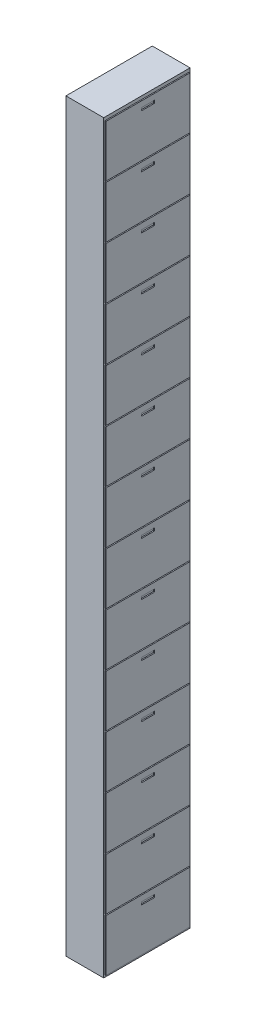
SolidWorks part; units mm, degrees
ref_plane "Front Plane" through (0, 0, 0) normal (0, 0, 1) x (1, 0, 0)
ref_plane "Top Plane" through (0, 0, 0) normal (0, 1, 0) x (1, 0, 0)
ref_plane "Right Plane" through (0, 0, 0) normal (1, 0, 0) x (0, 0, -1)
sketch "Sketch1" plane through (0, 0, 0) normal (0, 0, 1) x (1, 0, 0)
  line L0 (213.062, 4179.9863) -> (-136.938, 4179.9863)
  line L1 (-136.938, 4179.9863) -> (-136.938, -2720.0137)
  line L2 (-136.938, -2720.0137) -> (213.062, -2720.0137)
  line L5 (213.062, -2720.0137) -> (213.062, 4179.9863)
  dimension "D1" = 350
  dimension "D2" = 6900
extrude "Boss-Extrude1" add sketch "Sketch1" along normal blind 800
sketch "Sketch3" plane through (213.062, 0, 0) normal (1, 0, 0) x (0, 0, -1)
  line L0 (0, -2720.0137) -> (0, 4179.9863) construction
  line L1 (-790, -2700.0137) -> (-10, -2700.0137)
  line L2 (-790, -2700.0137) -> (-790, -2220.0137)
  line L3 (-790, -2220.0137) -> (-10, -2220.0137)
  line L4 (-10, -2700.0137) -> (-10, -2220.0137)
  line L5 (-800, -2720.0137) -> (0, -2720.0137) construction
  line L6 (-790, -2210.0137) -> (-10, -2210.0137)
  line L7 (-461.6648, -2274.1108) -> (-340.5919, -2274.1108)
  line L8 (-461.6648, -2274.1108) -> (-461.6648, -2299.9132)
  line L9 (-461.6648, -2299.9132) -> (-340.5919, -2299.9132)
  line L10 (-340.5919, -2274.1108) -> (-340.5919, -2299.9132)
  line L11 (-790, -2210.0137) -> (-790, -1730.0137)
  line L12 (-790, -1730.0137) -> (-10, -1730.0137)
  line L13 (-10, -2210.0137) -> (-10, -1730.0137)
  line L14 (-461.6648, -1784.1108) -> (-340.5919, -1784.1108)
  line L15 (-461.6648, -1809.9132) -> (-340.5919, -1809.9132)
  line L16 (-461.6648, -1784.1108) -> (-461.6648, -1809.9132)
  line L17 (-340.5919, -1784.1108) -> (-340.5919, -1809.9132)
  line L18 (-790, -1720.0137) -> (-10, -1720.0137)
  line L19 (-790, -1720.0137) -> (-790, -1240.0137)
  line L20 (-790, -1240.0137) -> (-10, -1240.0137)
  line L21 (-10, -1720.0137) -> (-10, -1240.0137)
  line L22 (-461.6648, -1294.1108) -> (-340.5919, -1294.1108)
  line L23 (-461.6648, -1319.9132) -> (-340.5919, -1319.9132)
  line L24 (-461.6648, -1294.1108) -> (-461.6648, -1319.9132)
  line L25 (-340.5919, -1294.1108) -> (-340.5919, -1319.9132)
  line L26 (-790, -1230.0137) -> (-10, -1230.0137)
  line L27 (-790, -1230.0137) -> (-790, -750.0137)
  line L28 (-790, -750.0137) -> (-10, -750.0137)
  line L29 (-10, -1230.0137) -> (-10, -750.0137)
  line L30 (-461.6648, -804.1108) -> (-340.5919, -804.1108)
  line L31 (-461.6648, -829.9132) -> (-340.5919, -829.9132)
  line L32 (-800, -2720.0137) -> (-800, 4179.9863) construction
  line L34 (-461.6648, -804.1108) -> (-461.6648, -829.9132)
  line L35 (-340.5919, -804.1108) -> (-340.5919, -829.9132)
  line L36 (-790, -740.0137) -> (-10, -740.0137)
  line L37 (-790, -740.0137) -> (-790, -260.0137)
  line L38 (-790, -260.0137) -> (-10, -260.0137)
  line L39 (-10, -740.0137) -> (-10, -260.0137)
  line L40 (-461.6648, -314.1108) -> (-340.5919, -314.1108)
  line L41 (-461.6648, -339.9132) -> (-340.5919, -339.9132)
  line L42 (-461.6648, -314.1108) -> (-461.6648, -339.9132)
  line L43 (-340.5919, -314.1108) -> (-340.5919, -339.9132)
  line L44 (-790, -250.0137) -> (-10, -250.0137)
  line L45 (-790, -250.0137) -> (-790, 229.9863)
  line L46 (-790, 229.9863) -> (-10, 229.9863)
  line L47 (-10, -250.0137) -> (-10, 229.9863)
  line L48 (-461.6648, 175.8892) -> (-340.5919, 175.8892)
  line L49 (-461.6648, 150.0868) -> (-340.5919, 150.0868)
  line L50 (-461.6648, 175.8892) -> (-461.6648, 150.0868)
  line L51 (-340.5919, 175.8892) -> (-340.5919, 150.0868)
  line L52 (-790, 239.9863) -> (-10, 239.9863)
  line L53 (-790, 239.9863) -> (-790, 719.9863)
  line L54 (-790, 719.9863) -> (-10, 719.9863)
  line L55 (-10, 239.9863) -> (-10, 719.9863)
  line L56 (-461.6648, 665.8892) -> (-340.5919, 665.8892)
  line L57 (-461.6648, 640.0868) -> (-340.5919, 640.0868)
  line L58 (-461.6648, 665.8892) -> (-461.6648, 640.0868)
  line L59 (-340.5919, 665.8892) -> (-340.5919, 640.0868)
  line L60 (-790, 729.9863) -> (-10, 729.9863)
  line L61 (-790, 729.9863) -> (-790, 1209.9863)
  line L62 (-790, 1209.9863) -> (-10, 1209.9863)
  line L63 (-10, 729.9863) -> (-10, 1209.9863)
  line L64 (-461.6648, 1155.8892) -> (-340.5919, 1155.8892)
  line L65 (-461.6648, 1130.0868) -> (-340.5919, 1130.0868)
  line L66 (-461.6648, 1155.8892) -> (-461.6648, 1130.0868)
  line L67 (-340.5919, 1155.8892) -> (-340.5919, 1130.0868)
  line L68 (-790, 1219.9863) -> (-10, 1219.9863)
  line L69 (-790, 1219.9863) -> (-790, 1699.9863)
  line L70 (-790, 1699.9863) -> (-10, 1699.9863)
  line L71 (-10, 1219.9863) -> (-10, 1699.9863)
  line L72 (-461.6648, 1645.8892) -> (-340.5919, 1645.8892)
  line L73 (-461.6648, 1620.0868) -> (-340.5919, 1620.0868)
  line L74 (-461.6648, 1645.8892) -> (-461.6648, 1620.0868)
  line L75 (-340.5919, 1645.8892) -> (-340.5919, 1620.0868)
  line L76 (-790, 1709.9863) -> (-10, 1709.9863)
  line L77 (-790, 1709.9863) -> (-790, 2189.9863)
  line L78 (-790, 2189.9863) -> (-10, 2189.9863)
  line L79 (-10, 1709.9863) -> (-10, 2189.9863)
  line L80 (-461.6648, 2135.8892) -> (-340.5919, 2135.8892)
  line L81 (-461.6648, 2110.0868) -> (-340.5919, 2110.0868)
  line L82 (-461.6648, 2135.8892) -> (-461.6648, 2110.0868)
  line L83 (-340.5919, 2135.8892) -> (-340.5919, 2110.0868)
  line L84 (-790, 2199.9863) -> (-10, 2199.9863)
  line L85 (-790, 2199.9863) -> (-790, 2679.9863)
  line L86 (-790, 2679.9863) -> (-10, 2679.9863)
  line L87 (-10, 2199.9863) -> (-10, 2679.9863)
  line L88 (-461.6648, 2625.8892) -> (-340.5919, 2625.8892)
  line L89 (-461.6648, 2600.0868) -> (-340.5919, 2600.0868)
  line L90 (-461.6648, 2625.8892) -> (-461.6648, 2600.0868)
  line L91 (-340.5919, 2625.8892) -> (-340.5919, 2600.0868)
  line L92 (-790, 2689.9863) -> (-10, 2689.9863)
  line L93 (-790, 2689.9863) -> (-790, 3169.9863)
  line L94 (-790, 3169.9863) -> (-10, 3169.9863)
  line L95 (-10, 2689.9863) -> (-10, 3169.9863)
  line L96 (-461.6648, 3115.8892) -> (-340.5919, 3115.8892)
  line L97 (-461.6648, 3090.0868) -> (-340.5919, 3090.0868)
  line L98 (-461.6648, 3115.8892) -> (-461.6648, 3090.0868)
  line L99 (-340.5919, 3115.8892) -> (-340.5919, 3090.0868)
  line L100 (-790, 3179.9863) -> (-10, 3179.9863)
  line L101 (-790, 3179.9863) -> (-790, 3659.9863)
  line L102 (-790, 3659.9863) -> (-10, 3659.9863)
  line L103 (-10, 3179.9863) -> (-10, 3659.9863)
  line L104 (-461.6648, 3605.8892) -> (-340.5919, 3605.8892)
  line L105 (-461.6648, 3580.0868) -> (-340.5919, 3580.0868)
  line L106 (-461.6648, 3605.8892) -> (-461.6648, 3580.0868)
  line L107 (-340.5919, 3605.8892) -> (-340.5919, 3580.0868)
  line L108 (-790, 3669.9863) -> (-10, 3669.9863)
  line L109 (-790, 3669.9863) -> (-790, 4149.9863)
  line L110 (-790, 4149.9863) -> (-10, 4149.9863)
  line L111 (-10, 3669.9863) -> (-10, 4149.9863)
  line L112 (-461.6648, 4095.8892) -> (-340.5919, 4095.8892)
  line L113 (-461.6648, 4070.0868) -> (-340.5919, 4070.0868)
  line L114 (-461.6648, 4095.8892) -> (-461.6648, 4070.0868)
  line L115 (-340.5919, 4095.8892) -> (-340.5919, 4070.0868)
  dimension "D1" = 480
  dimension "D2" = 10
  dimension "D3" = 20
  dimension "D4" = 14
  dimension "D6" = 10
  dimension "D5" = 10
extrude "Boss-Extrude3" add sketch "Sketch3" along normal blind 10 contours L1 L4 L3 L2 L7 L10 L9 L8 | L18 L21 L20 L19 L22 L25 L23 L24 | L6 L13 L12 L11 L14 L17 L15 L16 | L26 L29 L28 L27 L30 L35 L31 L34 | L36 L39 L38 L37 L40 L43 L41 L42 | L44 L47 L46 L45 L48 L51 L49 L50 | L52 L55 L54 L53 L56 L59 L57 L58 | L60 L63 L62 L61 L64 L67 L65 L66 | L68 L71 L70 L69 L72 L75 L73 L74 | L76 L79 L78 L77 L80 L83 L81 L82 | L84 L87 L86 L85 L88 L91 L89 L90 | L92 L95 L94 L93 L96 L99 L97 L98 | L100 L103 L102 L101 L104 L107 L105 L106 | L108 L111 L110 L109 L112 L115 L113 L114
